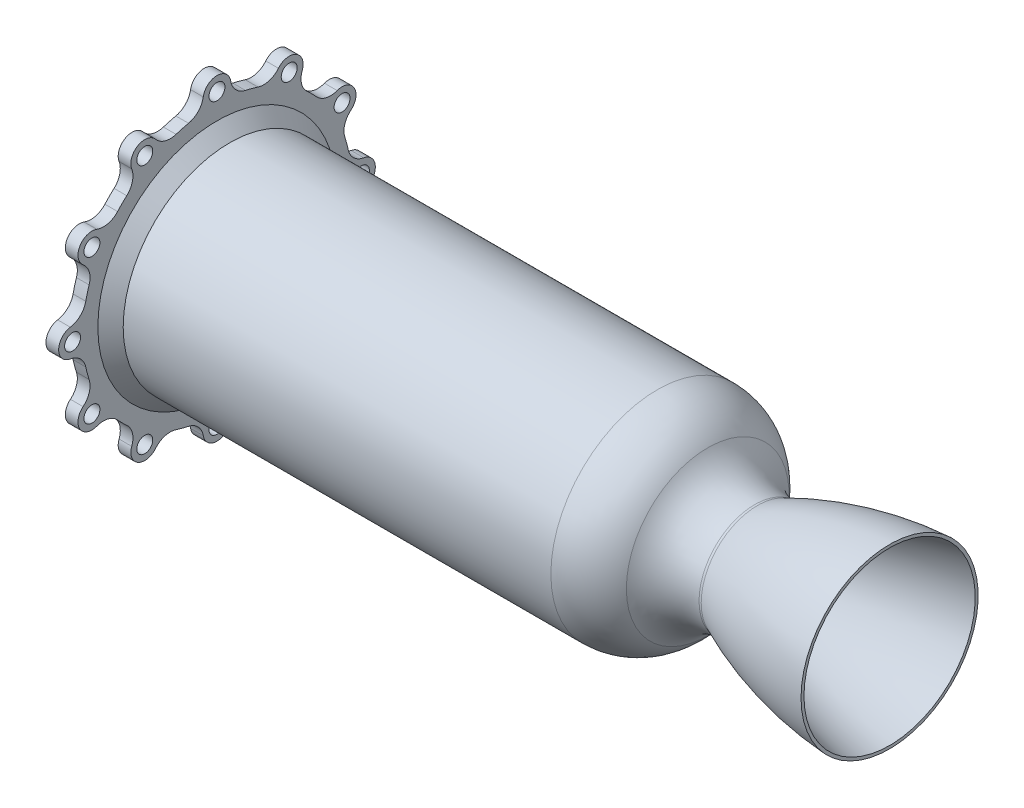
SolidWorks part; units mm, degrees
material "Inconel 718"
ref_plane "Front Plane" through (0, 0, 0) normal (0, 0, 1) x (1, 0, 0)
ref_plane "Top Plane" through (0, 0, 0) normal (0, 1, 0) x (1, 0, 0)
ref_plane "Right Plane" through (0, 0, 0) normal (1, 0, 0) x (0, 0, -1)
sketch "Sketch1" plane through (0, 0, 0) normal (0, 0, 1) x (1, 0, 0)
  line L0 (0, 21.5554) -> (67.3454, 21.5554) construction
  line L1 (0, 0) -> (0, 21.5554) construction
  line L2 (0, 21.5554) -> (0, 31.2726) construction
  line L3 (0, 21.5554) -> (0, 55.883) construction
  line L4 (0, 55.883) -> (0, 89.7945) construction
  line L5 (-275.8922, 0) -> (-275.8922, 59.723) construction
  line L6 (67.6057, 44.4) -> (67.6057, 42.9249)
  line L7 (-275.8922, 50.198) -> (-52.3722, 50.198)
  line L8 (-275.8922, 79.375) -> (-275.8922, 65.438)
  line L9 (-269.5422, 53.373) -> (-48.812, 53.373)
  line L10 (-269.5422, 53.373) -> (-269.5422, 79.375)
  line L11 (-236.4746, 0) -> (92.5965, 0) construction
  line L12 (-269.5422, 79.375) -> (-275.8922, 79.375)
  line L13 (-275.8922, 59.723) -> (-272.7172, 59.723)
  line L14 (-272.7172, 59.723) -> (-272.7172, 53.373)
  line L15 (-272.7172, 53.373) -> (-275.8922, 53.373)
  line L16 (-275.8922, 53.373) -> (-275.8922, 50.198)
  line L17 (-275.8922, 62.898) -> (-273.3522, 62.898)
  line L18 (-273.3522, 62.898) -> (-273.3522, 65.438)
  line L19 (-273.3522, 65.438) -> (-275.8922, 65.438)
  line L20 (-275.8922, 62.898) -> (-275.8922, 59.723)
  arc A0 (0, 21.5554) -> (3.6993, 22.2871) centre (0, 31.2726) ccw
  arc A1 (-28.9029, 37.3625) -> (0, 21.5554) centre (0, 55.883) ccw
  arc A2 (-28.9029, 37.3625) -> (-52.3722, 50.198) centre (-52.3722, 22.3239) ccw
  arc A3 (-23.5564, 40.7885) -> (0, 27.9054) centre (0, 55.883) ccw
  arc A4 (-48.812, 53.373) -> (-23.5564, 40.7885) centre (-48.812, 21.7382) cw
  arc A5 (0, 27.9054) -> (1.3746, 28.1987) centre (0, 31.2726) ccw
  arc A6 (1.3746, 28.1987) -> (67.6057, 44.4) centre (78.8554, -145.0667) cw
  spline S0 degree 4 poles (-2.3078, 19.3755) (-2.1205, 19.4699) (-1.7455, 19.6581) (-1.1811, 19.9396) (-0.4303, 20.3106) (0.3254, 20.6802) (1.0682, 21.0402) (1.8381, 21.4094) (2.5311, 21.7392) (3.5424, 22.2145) (4.0903, 22.4694) (5.427, 23.0866) (6.2853, 23.4736) (7.738, 24.1265) (8.9921, 24.6759) (10.3847, 25.2795) (11.7017, 25.8374) (12.7933, 26.2953) (14.1359, 26.8498) (15.7649, 27.5114) (17.6628, 28.2647) (19.8447, 29.1083) (22.0312, 29.9313) (24.2264, 30.7359) (26.4275, 31.5212) (28.6356, 32.2884) (31.2887, 33.1857) (34.5063, 34.2377) (37.7369, 35.2492) (40.9794, 36.2217) (43.786, 37.0337) (46.0358, 37.667) (48.2904, 38.2846) (50.5486, 38.8863) (52.8118, 39.4729) (55.0771, 40.044) (57.0654, 40.5314) (58.7672, 40.939) (60.1943, 41.2742) (61.3229, 41.5359) (62.4815, 41.8003) (63.5863, 42.0495) (64.7929, 42.3167) (65.8037, 42.5386) (67.374, 42.8763) (68.1776, 43.0465) (70.263, 43.4834) (71.2381, 43.6787) (72.6862, 43.9721) (73.3689, 44.1055) (73.7876, 44.188) (74.0054, 44.2309) knots 0 0 0 0 0 0.01043 0.02086 0.031289 0.041719 0.052023 0.062326 0.072629 0.082933 0.097451 0.111969 0.126487 0.141005 0.170041 0.184559 0.199077 0.213595 0.228113 0.25715 0.286186 0.315222 0.344258 0.373294 0.40233 0.431367 0.460403 0.512468 0.57054 0.599576 0.628612 0.657648 0.686685 0.715721 0.744757 0.773793 0.802829 0.817347 0.831865 0.846383 0.860902 0.87542 0.889938 0.904456 0.918974 0.93923 0.959487 0.979743 0.989872 1 1 1 1 1 construction
  spline S1 degree 4 poles (3.6993, 22.2871) (3.9207, 22.3903) (4.346, 22.5875) (5.427, 23.0866) (6.2853, 23.4736) (7.738, 24.1265) (8.9921, 24.6759) (10.3847, 25.2795) (11.7017, 25.8374) (12.7933, 26.2953) (14.1359, 26.8498) (15.7649, 27.5114) (17.6628, 28.2647) (19.8447, 29.1083) (22.0312, 29.9313) (24.2264, 30.7359) (26.4275, 31.5212) (28.6356, 32.2884) (31.2887, 33.1857) (34.5063, 34.2377) (37.7369, 35.2492) (40.9794, 36.2217) (43.786, 37.0337) (46.0358, 37.667) (48.2904, 38.2846) (50.5486, 38.8863) (52.8118, 39.4729) (55.0771, 40.044) (57.0654, 40.5314) (58.7672, 40.939) (60.1943, 41.2742) (61.3229, 41.5359) (62.4815, 41.8003) (63.5863, 42.0495) (64.7929, 42.3167) (65.8037, 42.5386) (66.8755, 42.7691) (67.3668, 42.8741) (67.6057, 42.9249) knots 0.082933 0.082933 0.082933 0.082933 0.082933 0.097451 0.111969 0.126487 0.141005 0.170041 0.184559 0.199077 0.213595 0.228113 0.25715 0.286186 0.315222 0.344258 0.373294 0.40233 0.431367 0.460403 0.512468 0.57054 0.599576 0.628612 0.657648 0.686685 0.715721 0.744757 0.773793 0.802829 0.817347 0.831865 0.846383 0.860902 0.87542 0.889938 0.904456 0.918974 0.918974 0.918974 0.918974 0.918974
  point P37 (-274.3047, 59.723)
  dimension "D1" = 6.35
  dimension "D3" = 23.4693
  dimension "D5" = 3.175
  dimension "D6" = 21.5554
  dimension "D7" = 42.9249
  dimension "D8" = 343.4979
  dimension "D10" = 31.6348
  dimension "D11" = 3.3673
  dimension "D9" = 189.8003
  dimension "D2" = 223.52
  dimension "D4" = 3.175
  dimension "D12" = 145.0667
  dimension "D13" = 63.9064
  dimension "D14" = 6.35
  dimension "D15" = 79.375
  dimension "D16" = 3.175
  dimension "D17" = 6.35
  dimension "D18" = 50.198
  dimension "D19" = 2.54
  dimension "D20" = 2.54
  dimension "D21" = 3.175
revolve "Revolve1" add sketch "Sketch1" angle 360 about L11
chamfer "Chamfer1" distance 6.35 angle 45 1 edges at (-269.5422, 0, 53.373)
fillet "Fillet1" radius 1.27 4 edges at (-275.8922, 0, 53.373) (-275.8922, 0, 50.198) (-272.7172, 0, 59.723) (-272.7172, 0, 53.373)
sketch "Sketch6" plane through (-275.8922, 0, 0) normal (-1, 0, 0) x (0, 0, 1)
  line L0 (0, 0) -> (0, 106.2653) construction
  circle A0 centre (0, 0) radius 72.39 construction
  point P3 (0, 72.39)
  point P8 (42.5498, 58.5647)
  point P9 (68.847, 22.3697)
  point P10 (68.847, -22.3697)
  point P11 (42.5498, -58.5647)
  point P12 (0, -72.39)
  point P13 (-42.5498, -58.5647)
  point P14 (-68.847, -22.3697)
  point P15 (-68.847, 22.3697)
  point P16 (-42.5498, 58.5647)
  point P17 (0, 0)
  dimension "D1" = 144.78
  dimension "D3" = 22.3697
  dimension "D4" = 68.847
  dimension "D2" = 10
hole_wizard "Hole2" positions "Sketch9" profile "Sketch10" legacy end condition up to next
sketch "Sketch9" plane through (-275.8922, 0, 0) normal (-1, 0, 0) x (0, 0, 1)
  line L0 (0, 0) -> (0, 72.39) construction
  point P0 (0, 72.39)
  dimension "D1" = 72.39
sketch "Sketch10" plane through (-275.8922, 72.39, 0) normal (0, 1, 0) x (0, 0, 1)
  line L0 (0, 0) -> (0, 6.351)
  line L1 (0, 6.351) -> (4, 6.351)
  line L2 (4, 6.351) -> (4, 0)
  line L3 (4, 0) -> (0, 0)
  line L4 (0, 110) -> (0, -10) construction
  dimension "Diameter" = 8
  dimension "Depth" = 6.351
pattern_circular "CirPattern3" count 12 over 360 about axis through (0, 0, 0) along (1, 0, 0) of "Hole2"
sketch "Sketch11" plane through (-275.8922, 0, 0) normal (-1, 0, 0) x (0, 0, 1)
  arc A0 (79.375, 0) -> (73.5318, 6.891) centre (72.39, 0) ccw
  circle A1 centre (0, 0) radius 79.375 construction
  arc A2 (79.375, 0) -> (68.7408, 39.6875) centre (0, 0) ccw
  arc A3 (67.1259, 30.7981) -> (68.7408, 39.6875) centre (62.6916, 36.195) ccw
  circle A4 centre (72.39, 0) radius 4 construction
  arc A5 (65.7802, 14.2688) -> (64.1017, 20.533) centre (0, 0) ccw
  arc A6 (65.7802, 14.2688) -> (73.5318, 6.891) centre (75.0887, 16.2879) ccw
  arc A7 (67.1259, 30.7981) -> (64.1017, 20.533) centre (73.1727, 23.4386) ccw
  circle A8 centre (62.6916, 36.195) radius 4 construction
  dimension "D1" = 19.05
  dimension "D2" = 67.31
extrude "Cut-Extrude1" cut sketch "Sketch11" against normal up to next (6.35 mm away)
pattern_circular "CirPattern4" count 12 over 360 about axis through (0, 0, 0) along (1, 0, 0) of "Cut-Extrude1"
